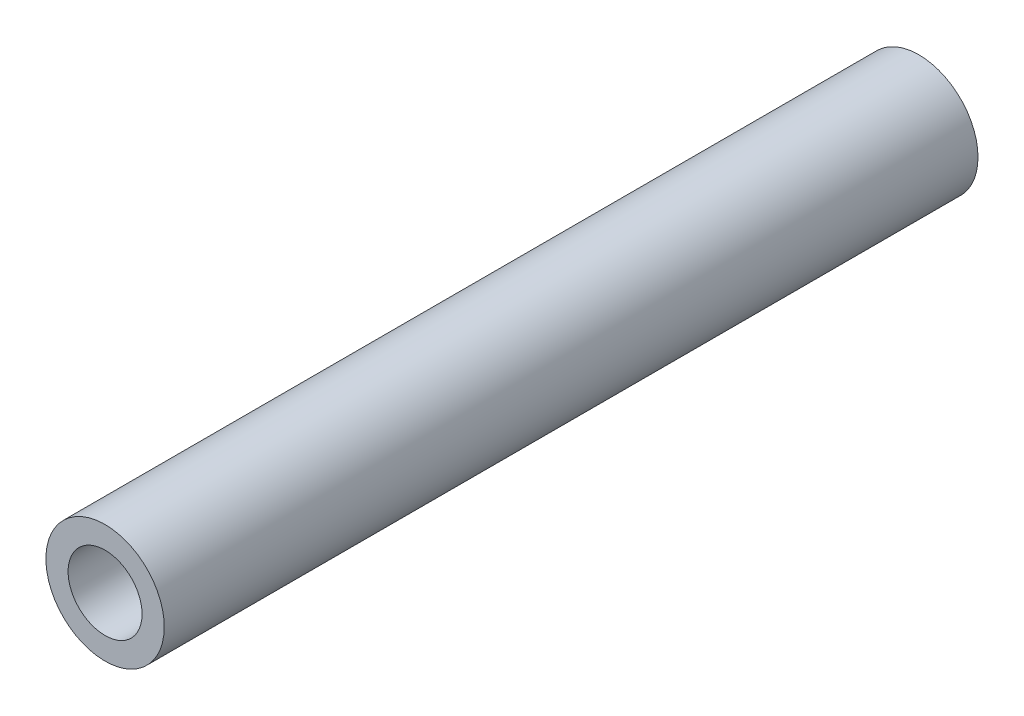
SolidWorks part; units mm, degrees
ref_plane "前视基准面" through (0, 0, 0) normal (0, 0, 1) x (1, 0, 0)
ref_plane "上视基准面" through (0, 0, 0) normal (0, 1, 0) x (1, 0, 0)
ref_plane "右视基准面" through (0, 0, 0) normal (1, 0, 0) x (0, 0, -1)
sketch "草图1" plane through (0, 0, 0) normal (0, 0, 1) x (1, 0, 0)
  circle A0 centre (0, 0) radius 1.6
  circle A1 centre (0, 0) radius 1
  dimension "D1" = 3.2
  dimension "D2" = 2
extrude "凸台-拉伸1" add sketch "草图1" along normal blind 22
